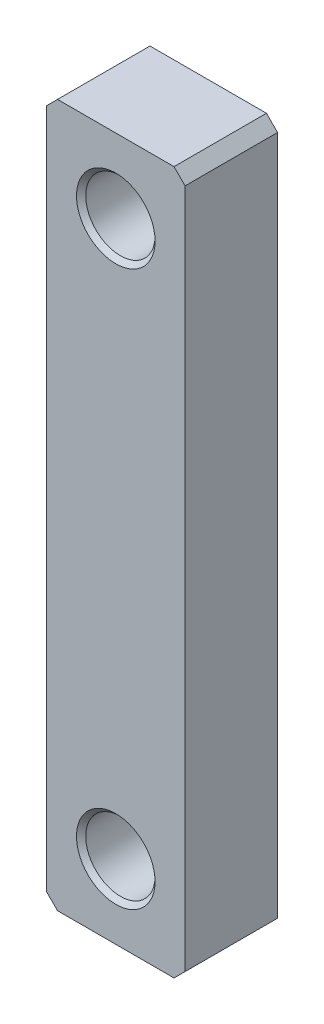
SolidWorks part; units mm, degrees
material "6061-T6 Al"
ref_plane "Front" through (0, 0, 0) normal (0, 0, 1) x (1, 0, 0)
ref_plane "Top" through (0, 0, 0) normal (0, 1, 0) x (1, 0, 0)
ref_plane "Right" through (0, 0, 0) normal (1, 0, 0) x (0, 0, -1)
sketch "Sketch1" plane through (0, 0, 0) normal (0, 0, 1) x (1, 0, 0)
  line L0 (-9.525, 48.26) -> (9.525, -48.26) construction
  line L2 (-9.525, 48.26) -> (9.525, 48.26)
  line L3 (-9.525, 48.26) -> (-9.525, -48.26)
  line L4 (-9.525, -48.26) -> (9.525, -48.26)
  line L5 (9.525, 48.26) -> (9.525, -48.26)
  dimension "D1" = 96.52
  dimension "D2" = 19.05
extrude "Boss-Extrude1" add sketch "Sketch1" against normal blind 12.7
hole_wizard "3/8-16 Tapped Hole1" positions "Sketch19" profile "Sketch18" tap size "3/8-16" standard "ANSI Inch"
sketch "Sketch19" plane through (-0.4611, -7.9891, 0) normal (0, 0, -1) x (-1, 0, 0)
  line L0 (-0.4611, -30.1109) -> (-0.4611, 7.9891) construction
  line L1 (-0.4611, 7.9891) -> (-0.4611, 46.0891) construction
  point P0 (-0.4611, -30.1109)
  point P2 (-0.4611, 46.0891)
  dimension "D1" = 76.2
sketch "Sketch18" plane through (0, -38.1, 0) normal (1, 0, 0) x (0, -1, 0)
  line L0 (0, 0) -> (0, 29.3849)
  line L1 (0, 29.3849) -> (3.9687, 27.0002)
  line L2 (3.9687, 27.0002) -> (3.9687, 19.05)
  line L3 (3.9687, 19.05) -> (4.7625, 19.05)
  line L5 (4.7625, 19.05) -> (4.7625, 0.635)
  line L6 (4.7625, 0.635) -> (5.3975, 0)
  line L7 (5.3975, 0) -> (0, 0)
  line L8 (-4.7625, 0.635) -> (-5.3975, 0) construction
  line L10 (0, 29.3849) -> (-3.9688, 27.0002) construction
  line L11 (0, -6.35) -> (0, 107.95) construction
  dimension "Tap Drill Dia." = 7.9375
  dimension "Tap Drill Depth" = 27.0002
  dimension "Thread Major Dia." = 9.525
  dimension "Thread Depth" = 19.05
  dimension "Near C'Sink Dia." = 10.795
  dimension "Near C'Sink Angle" = 90
  dimension "Drill Angle" = 118
chamfer "Chamfer1" distance 1.524 angle 45 4 edges at (9.525, -48.26, -6.35) (-9.525, -48.26, -6.35) (-9.525, 48.26, -6.35) (9.525, 48.26, -6.35)
